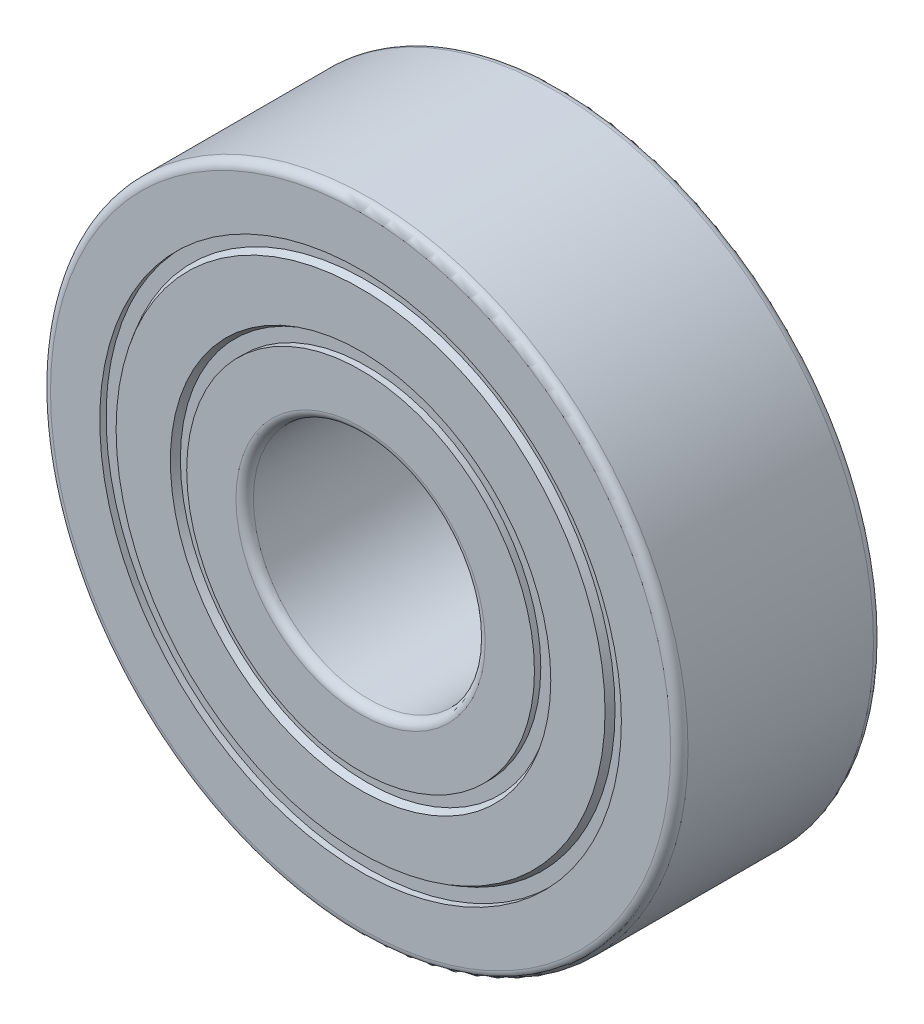
SolidWorks part; units mm, degrees
ref_plane "Plane1" through (0, 0, 0) normal (0, 0, 1) x (1, 0, 0)
ref_plane "Plane2" through (0, 0, 0) normal (0, 1, 0) x (1, 0, 0)
ref_plane "Plane3" through (0, 0, 0) normal (1, 0, 0) x (0, 0, -1)
sketch "Sketch2" plane through (0, 0, 0) normal (0, 1, 0) x (1, 0, 0)
  line L0 (0, -19) -> (0, 31) construction
  line L1 (-9, 0) -> (-9, -0.2188)
  line L2 (-4.3, -7) -> (-6, -7)
  line L3 (-4, -6.7) -> (-4, -0.3)
  line L4 (-4.3, 0) -> (-6, 0)
  line L5 (-11, -6.7) -> (-11, -0.3)
  line L6 (-9, -7) -> (-9, -6.7812)
  line L7 (-9, 0) -> (-10.7, 0)
  line L8 (-9, -7) -> (-10.7, -7)
  line L9 (-11, -3.5) -> (-4, -3.5) construction
  line L10 (-9, -0.2188) -> (-8.5625, -0.2188)
  line L11 (-9, -6.7812) -> (-8.5625, -6.7812)
  line L12 (-8.5625, -0.2188) -> (-8.4362, 0)
  line L13 (-8.5625, -6.7812) -> (-8.4362, -7)
  line L14 (-6, 0) -> (-6, -0.2188)
  line L15 (-6, -7) -> (-6, -6.7812)
  line L16 (-8.4362, -7) -> (-6.5638, -7)
  line L17 (-8.4362, 0) -> (-6.5638, 0)
  line L18 (-6, -0.2188) -> (-6.4375, -0.2188)
  line L19 (-6, -6.7812) -> (-6.4375, -6.7812)
  line L20 (-6.4375, -0.2188) -> (-6.5638, 0)
  line L21 (-6.4375, -6.7812) -> (-6.5638, -7)
  line L26 (-4.3, -7) -> (-4.2, -7) construction
  line L27 (-4.3, 0) -> (-4.2, 0) construction
  line L28 (-4, -6.8) -> (-4, -6.7) construction
  line L29 (-4, -0.2) -> (-4, -0.3) construction
  line L30 (-11, -6.7) -> (-11, -6.8) construction
  line L31 (-10.8, -7) -> (-10.7, -7) construction
  line L32 (-11, -0.3) -> (-11, -0.2) construction
  line L33 (-10.8, 0) -> (-10.7, 0) construction
  arc A0 (-11, -0.3) -> (-10.7, 0) centre (-10.7, -0.3) cw
  arc A1 (-11, -6.7) -> (-10.7, -7) centre (-10.7, -6.7) ccw
  arc A2 (-4, -6.7) -> (-4.3, -7) centre (-4.3, -6.7) cw
  arc A3 (-4.3, 0) -> (-4, -0.3) centre (-4.3, -0.3) cw
  arc A4 (-4, -6.8) -> (-4.2, -7) centre (-4.2, -6.8) cw construction
  arc A5 (-4, -0.2) -> (-4.2, 0) centre (-4.2, -0.2) ccw construction
  arc A6 (-10.8, -7) -> (-11, -6.8) centre (-10.8, -6.8) cw construction
  arc A7 (-10.8, 0) -> (-11, -0.2) centre (-10.8, -0.2) ccw construction
  circle A8 centre (-7.5, -3.5) radius 2.1875
  dimension "r" = 0.3
  dimension "BallDia" = 4.375
  dimension "B" = 7
  dimension "D4" = 6.5625
  dimension "ID" = 8
  dimension "OD" = 22
  dimension "D5" = 6.5625
  dimension "OR-ID" = 18
  dimension "IR-OD" = 12
  dimension "Shield-OD" = 0.4375
  dimension "D9" = 60
  dimension "Shield-ID" = 0.4375
  dimension "D11" = 60
revolve "Base-Revolve" add sketch "Sketch2" angle 360 about L0
ref_plane "Plane4" through (0, 0, 3.5) normal (0, 0, 1) x (1, 0, 0)
equation "\"D5@Sketch2\"=\"B@Sketch2\" * .9375"
equation "\"D4@Sketch2\" = \"D5@Sketch2\""
equation "\"BallDia@Sketch2\" = \"B@Sketch2\" * .625"
equation "\"Shield-OD@Sketch2\" = (\"OD@Sketch2\"-\"ID@Sketch2\") * 0.03125"
equation "\"Shield-ID@Sketch2\" = \"Shield-OD@Sketch2\""
